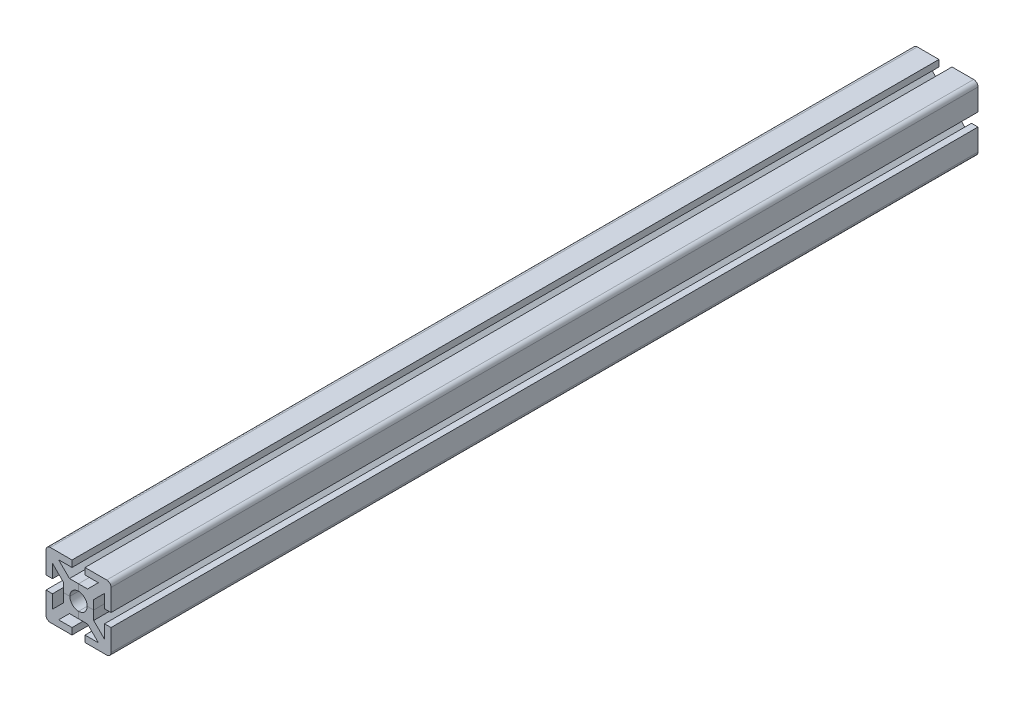
SolidWorks part; units mm, degrees
ref_plane "Alzado" through (0, 0, 0) normal (0, 0, 1) x (1, 0, 0)
ref_plane "Planta" through (0, 0, 0) normal (0, 1, 0) x (1, 0, 0)
ref_plane "Vista lateral" through (0, 0, 0) normal (1, 0, 0) x (0, 0, -1)
sketch "Croquis1" plane through (0, 0, 0) normal (0, 0, 1) x (1, 0, 0)
  line L0 (0, 0) -> (50000, 0) construction
  line L1 (-15, 15) -> (15, 15) construction
  line L2 (-15, 15) -> (-15, -15) construction
  line L3 (-15, -15) -> (15, -15) construction
  line L4 (15, 15) -> (15, -15) construction
  line L5 (-15, 15) -> (15, -15) construction
  line L6 (-15, -15) -> (15, 15) construction
  line L7 (0, 0) -> (0, -50000) construction
  line L8 (0, 4) -> (0, 7)
  line L9 (0, 7) -> (4.1716, 7)
  line L10 (4.1716, 7) -> (9.1716, 12)
  line L11 (9.1716, 12) -> (3, 12)
  line L12 (3, 12) -> (3, 15)
  line L13 (3, 15) -> (15, 15)
  line L20 (2.8284, 2.8284) -> (15, 15)
  arc A0 (2.8284, 2.8284) -> (0, 4) centre (0, 0) ccw
  point P0 (0, 0)
  point P13 (0, 3)
  dimension "D3" = 4
  dimension "D1" = 30
  dimension "D2" = 6
  dimension "D4" = 8
  dimension "D5" = 3
  dimension "D6" = 2
extrude "Saliente-Extruir1" add sketch "Croquis1" along normal mid plane 400
mirror "Simetría1" about plane through (2.8284, 2.8284, 200) normal (-0.7071, 0.7071, 0) of "Saliente-Extruir1"
fillet "Redondeo1" radius 2 1 edges at (15, 15, 0)
pattern_circular "MatrizC4" count 4 over 360 about axis through (0, 0, 0) along (0, 0, 1) of bodies 102
